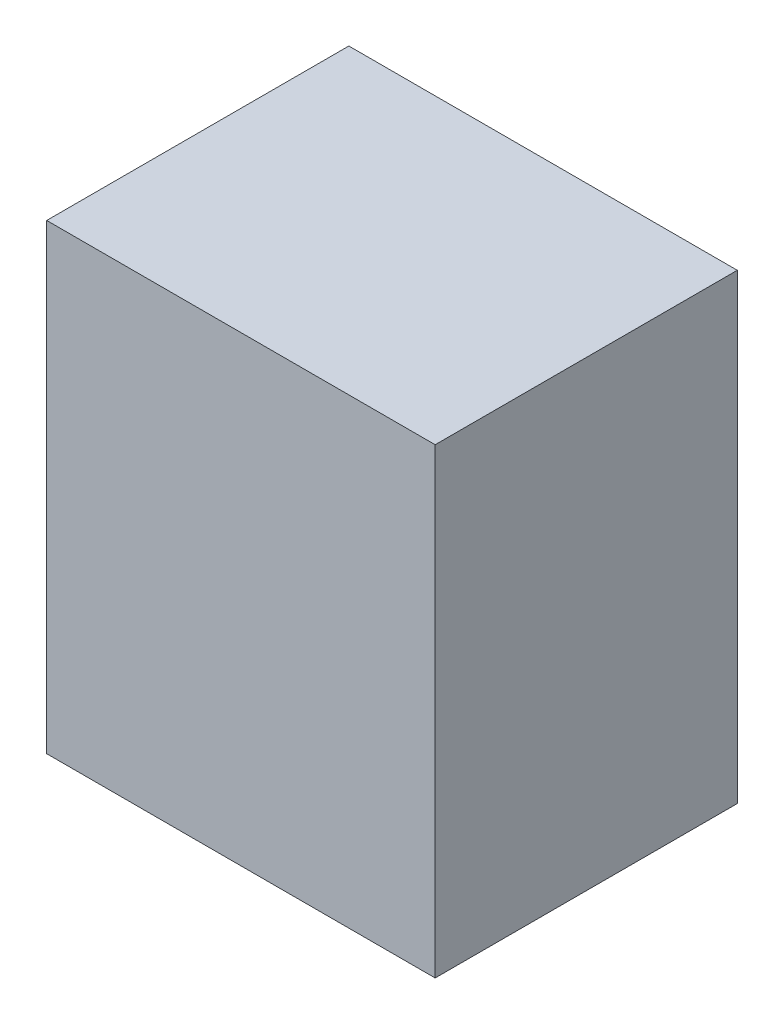
SolidWorks part; units mm, degrees
ref_plane "Front Plane" through (0, 0, 0) normal (0, 0, 1) x (1, 0, 0)
ref_plane "Top Plane" through (0, 0, 0) normal (0, 1, 0) x (1, 0, 0)
ref_plane "Right Plane" through (0, 0, 0) normal (1, 0, 0) x (0, 0, -1)
sketch "Sketch1" plane through (0, 0, 0) normal (0, 1, 0) x (1, 0, 0)
  line L1 (0, 0) -> (90, 0)
  line L2 (0, 0) -> (0, 70)
  line L3 (0, 70) -> (90, 70)
  line L4 (90, 0) -> (90, 70)
  dimension "D1" = 90
  dimension "D2" = 70
extrude "Boss-Extrude1" add sketch "Sketch1" along normal blind 107
